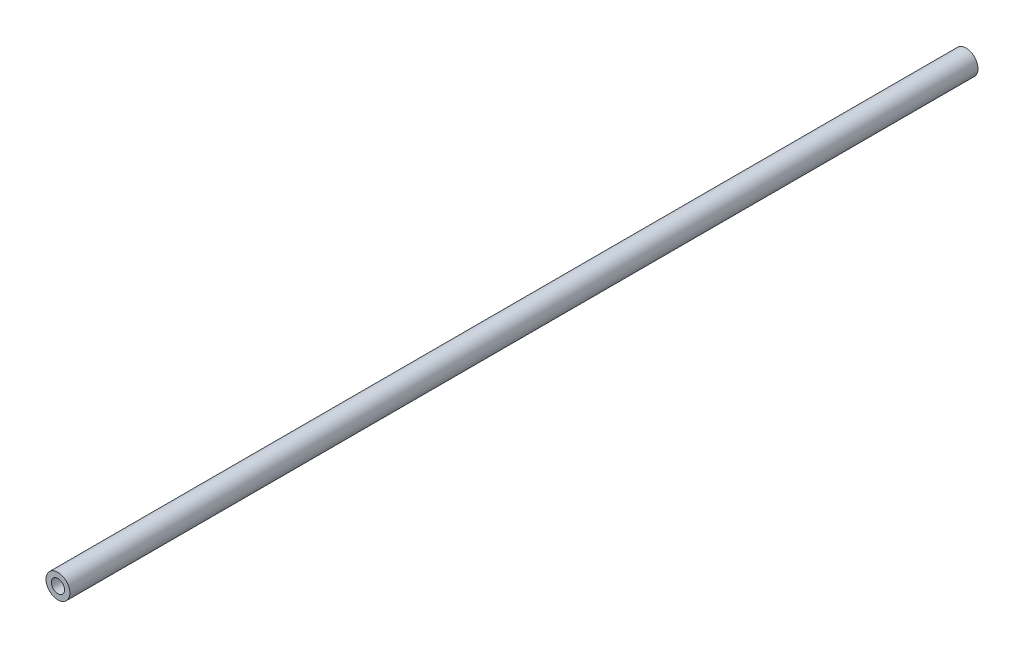
SolidWorks part; units mm, degrees
material "6061-T6 (SS)"
ref_plane "Front Plane" through (0, 0, 0) normal (0, 0, 1) x (1, 0, 0)
ref_plane "Top Plane" through (0, 0, 0) normal (0, 1, 0) x (1, 0, 0)
ref_plane "Right Plane" through (0, 0, 0) normal (1, 0, 0) x (0, 0, -1)
sketch "Sketch1" plane through (0, 0, 0) normal (0, 0, 1) x (1, 0, 0)
  circle A0 centre (0, 0) radius 3.175
  dimension "D1" = 6.35
extrude "Boss-Extrude1" add sketch "Sketch1" along normal blind 241.3
hole_wizard "#6-32 Tapped Hole1" positions "Sketch3" profile "Sketch2" tap size "#6-32" standard "Ansi Inch"
sketch "Sketch3" plane through (0, 0, 241.3) normal (0, 0, 1) x (1, 0, 0)
  line L0 (0, 3.175) -> (0, -3.175) construction
  circle A0 centre (0, 0) radius 3.175 construction
  point P0 (0, 0)
sketch "Sketch2" plane through (0, 0, 241.3) normal (1, 0, 0) x (0, -1, 0)
  line L0 (0, 0) -> (0, 10.2107)
  line L1 (0, 10.2107) -> (1.3525, 9.398)
  line L2 (1.3525, 9.398) -> (1.3525, 7.112)
  line L3 (1.3525, 7.112) -> (1.7526, 7.112)
  line L4 (1.7526, 7.112) -> (1.7526, 0)
  line L5 (1.7526, 0) -> (0, 0)
  line L10 (0, 10.2107) -> (-1.3526, 9.398) construction
  line L11 (0, -6.35) -> (0, 107.95) construction
  dimension "Tap Drill Dia." = 2.7051
  dimension "Tap Drill Depth" = 9.398
  dimension "Thread Major Dia." = 3.5052
  dimension "Thread Depth" = 7.112
  dimension "Drill Angle" = 118
hole_wizard "#6-32 Tapped Hole2" positions "Sketch5" profile "Sketch4" tap size "#6-32" standard "Ansi Inch"
sketch "Sketch5" plane through (0, 0, 0) normal (0, 0, -1) x (-1, 0, 0)
  line L0 (0, 3.175) -> (0, -3.175) construction
  circle A0 centre (0, 0) radius 3.175 construction
  point P0 (0, 0)
sketch "Sketch4" plane through (0, 0, 0) normal (1, 0, 0) x (0, 1, 0)
  line L0 (0, 0) -> (0, 10.2107)
  line L1 (0, 10.2107) -> (1.3525, 9.398)
  line L2 (1.3525, 9.398) -> (1.3525, 7.112)
  line L3 (1.3525, 7.112) -> (1.7526, 7.112)
  line L4 (1.7526, 7.112) -> (1.7526, 0)
  line L5 (1.7526, 0) -> (0, 0)
  line L10 (0, 10.2107) -> (-1.3526, 9.398) construction
  line L11 (0, -6.35) -> (0, 107.95) construction
  dimension "Tap Drill Dia." = 2.7051
  dimension "Tap Drill Depth" = 9.398
  dimension "Thread Major Dia." = 3.5052
  dimension "Thread Depth" = 7.112
  dimension "Drill Angle" = 118
